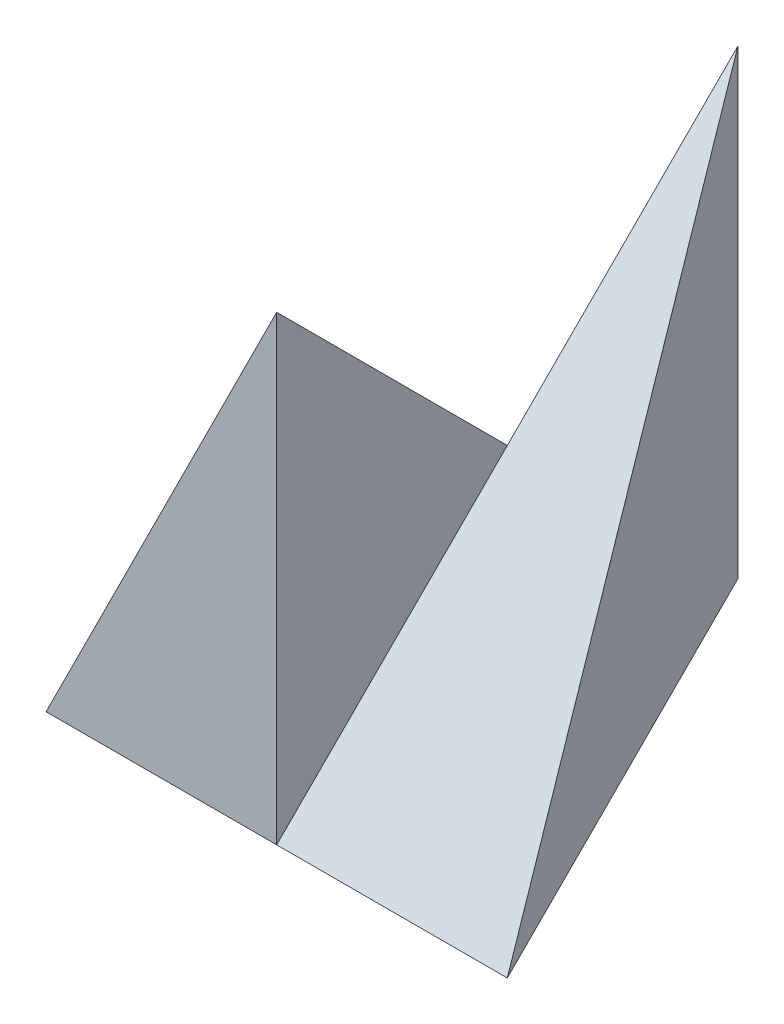
SolidWorks part; units mm, degrees
ref_plane "Front" through (0, 0, 0) normal (0, 0, 1) x (1, 0, 0)
ref_plane "Top" through (0, 0, 0) normal (0, 1, 0) x (1, 0, 0)
ref_plane "Right" through (0, 0, 0) normal (1, 0, 0) x (0, 0, -1)
sketch "Sketch1" plane through (0, 0, 0) normal (0, 1, 0) x (1, 0, 0)
  line L1 (-2, -2) -> (2, -2)
  line L2 (-2, -2) -> (-2, 2)
  line L3 (-2, 2) -> (2, 2)
  line L4 (2, -2) -> (2, 2)
  line L5 (-2, -2) -> (2, 2) construction
  line L6 (-2, 2) -> (2, -2) construction
  point P0 (0, 0)
  dimension "D1" = 4
  dimension "D2" = 4
extrude "Boss-Extrude1" add sketch "Sketch1" along normal blind 4
sketch "Sketch2" plane through (-2, 0, 0) normal (-1, 0, 0) x (0, 0, 1)
  line L0 (2, 4) -> (-2, 0)
  line L1 (-2, 0) -> (-2, 4)
  line L2 (-2, 4) -> (2, 4)
extrude "Cut-Extrude1" cut sketch "Sketch2" against normal blind 2
sketch "Sketch3" plane through (2, 0, 0) normal (1, 0, 0) x (0, 0, -1)
  line L0 (-2, 0) -> (2, 4)
  line L1 (2, 4) -> (-2, 4)
  line L2 (-2, 4) -> (-2, 0)
extrude "Cut-Extrude2" cut sketch "Sketch3" against normal blind 2
sketch "Sketch4" plane through (0, 0, 2) normal (0, 0, 1) x (1, 0, 0)
  line L0 (-2, 0) -> (0, 4)
  line L1 (0, 4) -> (2, 0)
  line L2 (2, 0) -> (2, 4)
  line L3 (2, 4) -> (-2, 4)
  line L4 (-2, 4) -> (-2, 0)
  line M3 (0, 4) -> (-2, 4)
  line M4 (-2, 4) -> (-2, 0)
extrude "Cut-Extrude3" cut sketch "Sketch4" against normal blind 10 contours L0 M4 M3 | L2 L3 L1
sketch "Sketch5" plane through (0, 0, 0) normal (0, -1, 0) x (1, 0, 0)
  line L0 (2, 2) -> (0, -2)
  line L1 (0, -2) -> (-2, 2)
  line L2 (-2, 2) -> (-2, -2)
  line L3 (-2, -2) -> (2, -2)
  line L4 (2, -2) -> (2, 2)
  line M1 (2, -2) -> (2, 2)
  line M4 (-2, 2) -> (-2, -2)
  line M5 (-2, -2) -> (0, -2)
  line M6 (0, -2) -> (2, -2)
extrude "Cut-Extrude4" cut sketch "Sketch5" against normal blind 10 contours L0 M1 M6 | L1 M5 M4
